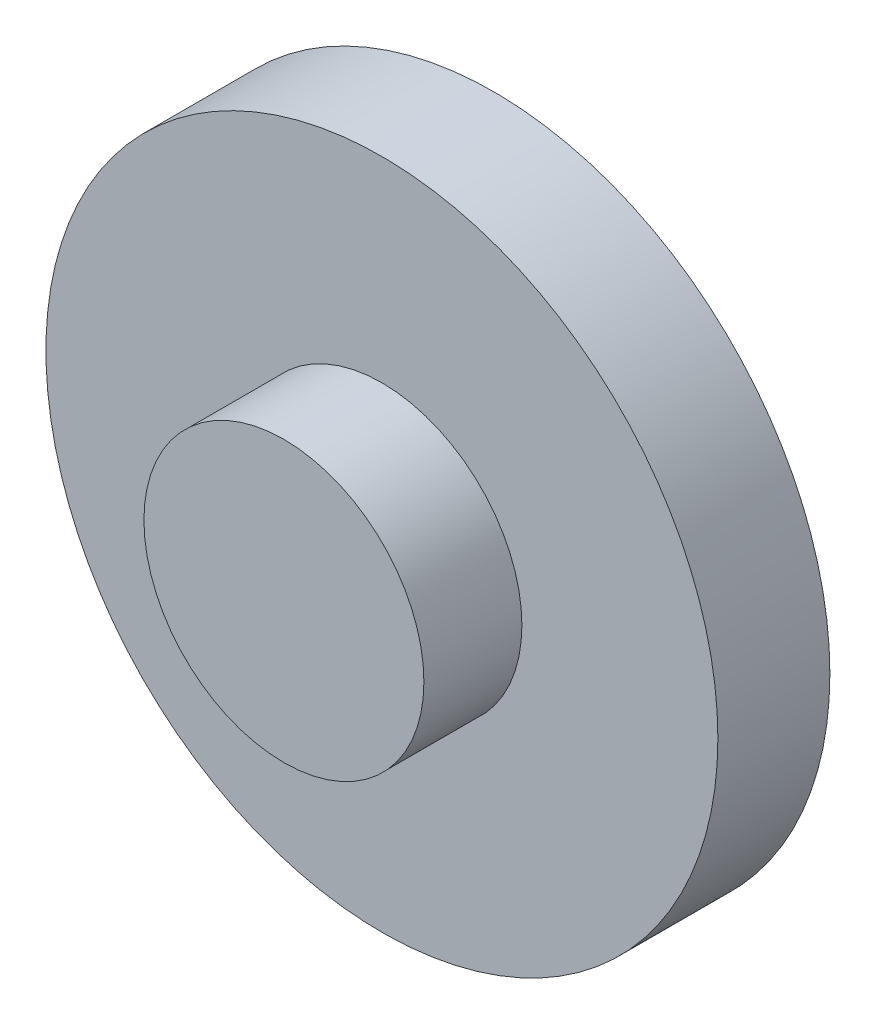
SolidWorks part; units mm, degrees
ref_plane "Front Plane" through (0, 0, 0) normal (0, 0, 1) x (1, 0, 0)
ref_plane "Top Plane" through (0, 0, 0) normal (0, 1, 0) x (1, 0, 0)
ref_plane "Right Plane" through (0, 0, 0) normal (1, 0, 0) x (0, 0, -1)
sketch "Sketch1" plane through (0, 0, 0) normal (0, 0, 1) x (1, 0, 0)
  circle A0 centre (0, 0) radius 76.2
  circle A1 centre (0, 0) radius 15.875
  dimension "D1" = 152.4
  dimension "D2" = 31.75
extrude "Boss-Extrude1" add sketch "Sketch1" along normal blind 25.4
sketch "Sketch2" plane through (0, 0, 25.4) normal (0, 0, 1) x (1, 0, 0)
  circle A0 centre (0, 0) radius 31.75
  dimension "D1" = 63.5
extrude "Boss-Extrude2" add sketch "Sketch2" along normal blind 22.225
